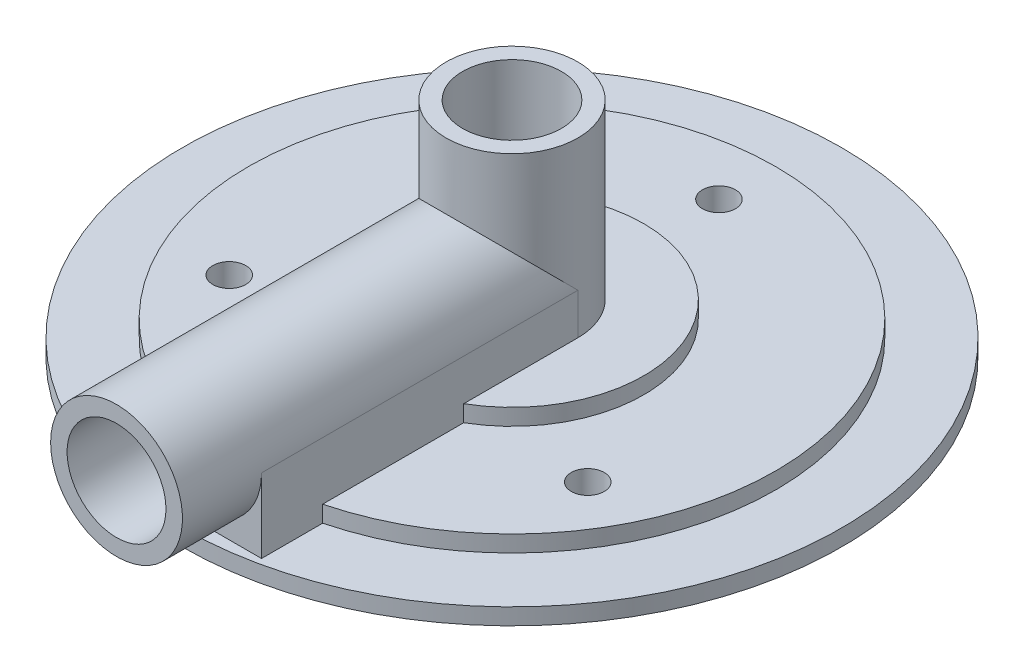
SolidWorks part; units mm, degrees
ref_plane "Alzado" through (0, 0, 0) normal (0, 0, 1) x (1, 0, 0)
ref_plane "Planta" through (0, 0, 0) normal (0, 1, 0) x (1, 0, 0)
ref_plane "Vista lateral" through (0, 0, 0) normal (1, 0, 0) x (0, 0, -1)
sketch "Sketch1" plane through (0, 0, 0) normal (0, 0, 1) x (1, 0, 0)
  line L0 (0, 0) -> (0, 28.6436) construction
  line L1 (0, 0) -> (43.1085, 0) construction
  line L2 (0, 20.6375) -> (6.35, 20.6375)
  line L3 (6.35, 20.6375) -> (6.35, 3.9688)
  line L4 (6.35, 3.9688) -> (12.7, 3.9688)
  line L5 (12.7, 3.9688) -> (12.7, 2.3812)
  line L6 (12.7, 2.3812) -> (25.4, 2.3812)
  line L7 (25.4, 2.3812) -> (25.4, 0.7937)
  line L8 (25.4, 0.7937) -> (31.75, 0.7937)
  line L9 (31.75, 0.7937) -> (31.75, -0.7937)
  line L10 (12.7, -3.9688) -> (12.7, -2.3812)
  line L11 (25.4, -2.3812) -> (25.4, -0.7937)
  line L12 (25.4, -0.7937) -> (31.75, -0.7937)
  line L13 (12.7, -2.3812) -> (25.4, -2.3812)
  line L14 (6.35, -3.9688) -> (12.7, -3.9688)
  line L15 (6.35, -3.9688) -> (0, -3.9688)
  line L16 (0, 20.6375) -> (0, -3.9688)
  point P6 (12.7, 3.175)
  point P15 (31.75, 0)
  point P20 (43.1085, 0)
  point P22 (0, 28.6436)
  point P23 (0, 0)
  dimension "D1" = 6.35
  dimension "D2" = 20.6375
  dimension "D3" = 0.7937
  dimension "D4" = 1.5875
  dimension "D5" = 1.5875
  dimension "D6" = 12.7
  dimension "D7" = 25.4
  dimension "D8" = 31.75
revolve "Revolve1" add sketch "Sketch1" angle 360 about L16
sketch3d "3DSketch1"
  point P5 (0, 7.9375, 0)
  dimension "D1" = 7.9375
sketch "Sketch3" plane through (0, 7.9375, 0) normal (0, 1, 0) x (1, 0, 0)
  line L0 (0, 0) -> (0, -29.6267) construction
  line L2 (0, 0) -> (6.35, 0)
  line L3 (0, 0) -> (0, -38.1)
  line L4 (0, -38.1) -> (6.35, -38.1)
  line L5 (6.35, 0) -> (6.35, -38.1)
  dimension "D1" = 6.35
  dimension "D2" = 38.1
revolve "Revolve2" add sketch "Sketch3" angle 360 about L0
sketch3d "3DSketch2" plane through (0, 0, 0) normal (0, 0, 1) x (1, 0, 0)
  dimension "D1" = 7.62
sketch "Sketch4" plane through (0, 0, 30.48) normal (0, 0, 1) x (1, 0, 0)
  line L0 (6.35, 7.9375) -> (6.35, 0.7937)
  line L1 (-6.35, 7.9375) -> (-6.35, 0.7937)
  line L2 (-6.35, 0.7937) -> (6.35, 0.7937)
  line L4 (31.75, 0.7937) -> (-31.75, 0.7937) construction
  circle A2 centre (0, 7.9375) radius 6.35 construction
  circle A3 centre (0, 7.9375) radius 6.35 construction
extrude "Extrude-Thin1" add sketch "Sketch4" against normal up to next thin
hole_wizard "Hole1" positions "Sketch5" profile "Sketch6" legacy
sketch "Sketch5" plane through (0, 0, 38.1) normal (0, 0, 1) x (1, 0, 0)
  point P0 (0, 7.9375)
  dimension "D1" = 7.9375
sketch "Sketch6" plane through (0, 7.9375, 38.1) normal (1, 0, 0) x (0, -1, 0)
  line L0 (0, 0) -> (0, 38.1)
  line L1 (0, 38.1) -> (4.7625, 38.1)
  line L2 (4.7625, 38.1) -> (4.7625, 0)
  line L3 (4.7625, 0) -> (0, 0)
  line L4 (0, 110) -> (0, -10) construction
  dimension "Diameter" = 9.525
  dimension "Depth" = 38.1
hole_wizard "Hole2" positions "Sketch7" profile "Sketch8" legacy end condition through all
sketch "Sketch7" plane through (0, 20.6375, 0) normal (0, 1, 0) x (1, 0, 0)
  point P0 (0, 0)
sketch "Sketch8" plane through (0, 20.6375, 0) normal (1, 0, 0) x (0, 0, 1)
  line L0 (0, 0) -> (0, 24.6063)
  line L1 (0, 24.6063) -> (4.7625, 24.6063)
  line L2 (4.7625, 24.6063) -> (4.7625, 0)
  line L3 (4.7625, 0) -> (0, 0)
  line L4 (0, 110) -> (0, -10) construction
  dimension "Diameter" = 9.525
  dimension "Depth" = 24.6063
hole_wizard "Hole3" positions "Sketch9" profile "Sketch10" legacy end condition through all
sketch "Sketch9" plane through (0, 2.3812, 0) normal (0, 1, 0) x (1, 0, 0)
  circle A0 centre (0, 0) radius 19.939 construction
  point P0 (0, 19.939)
  point P23 (17.2677, -9.9695)
  point P24 (-17.2677, -9.9695)
  dimension "D1" = 39.878
  dimension "D2" = 3
sketch "Sketch10" plane through (0, 2.3812, -19.939) normal (1, 0, 0) x (0, 0, 1)
  line L0 (0, 0) -> (0, 6.35)
  line L1 (0, 6.35) -> (1.5875, 6.35)
  line L2 (1.5875, 6.35) -> (1.5875, 0)
  line L3 (1.5875, 0) -> (0, 0)
  line L4 (0, 110) -> (0, -10) construction
  dimension "Diameter" = 3.175
  dimension "Depth" = 6.35
